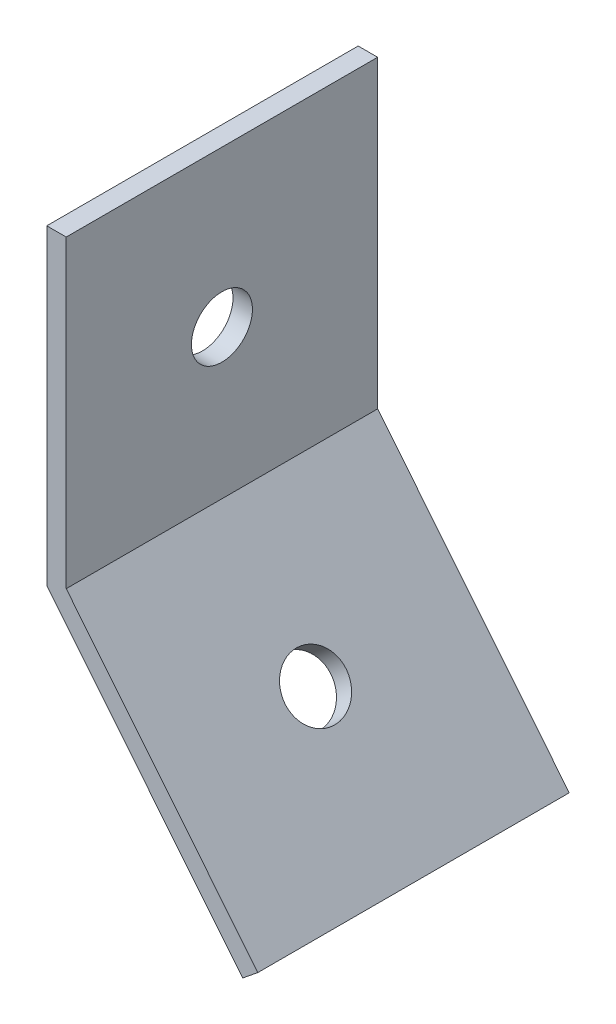
SolidWorks part; units mm, degrees
ref_plane "Front Plane" through (0, 0, 0) normal (0, 0, 1) x (1, 0, 0)
ref_plane "Top Plane" through (0, 0, 0) normal (0, 1, 0) x (1, 0, 0)
ref_plane "Right Plane" through (0, 0, 0) normal (1, 0, 0) x (0, 0, -1)
sketch "Sketch1" plane through (0, 0, 0) normal (0, 0, 1) x (1, 0, 0)
  line L0 (50.8, 762) -> (50.8, 736.6)
  line L1 (50.8, 1244.6) -> (50.8, 0) construction
  line L2 (50.8, 736.6) -> (66.782, 716.8583)
  line L3 (660.4, -16.4074) -> (50.8, 736.6) construction
  dimension "D1" = 25.4
extrude "Extrude-Thin1" add sketch "Sketch1" against normal blind 25.4 thin thin type one direction reverse wall 1.5875
ref_plane "Plane1" through (-226.0806, 638.5731, 0) normal (0.3337, -0.9427, 0) x (-0.9427, -0.3337, 0)
hole_wizard "#9 (0.196) Diameter Hole1" positions "Sketch6" profile "Sketch7" hole size "#9" standard "ANSI Inch" end condition up to next
sketch "Sketch6" plane through (392.1522, 317.4683, 0) normal (0.7772, 0.6292, 0) x (0, 0, -1)
  line L0 (0, 539.9841) -> (0, 515.1462) construction
  line L1 (25.4, 515.1462) -> (0, 515.1462) construction
  point P0 (12.7, 527.8462)
  dimension "D1" = 12.7
  dimension "D2" = 12.7
sketch "Sketch7" plane through (60.0249, 727.728, -12.7) normal (0, 0, 1) x (-0.6292, 0.7772, 0)
  line L0 (0, 0) -> (0, 1.5885)
  line L1 (0, 1.5885) -> (2.4892, 1.5885)
  line L2 (2.4892, 1.5885) -> (2.4892, 0)
  line L5 (2.4892, 0) -> (0, 0)
  line L11 (0, -6.35) -> (0, 107.95) construction
  dimension "Thru Hole Dia." = 4.9784
  dimension "Thru Hole Depth" = 1.5885
mirror "Mirror1" about plane through (-226.0806, 638.5731, 0) normal (0.3337, -0.9427, 0) of "#9 (0.196) Diameter Hole1"
equation "\"Thick\"= \"in\""
